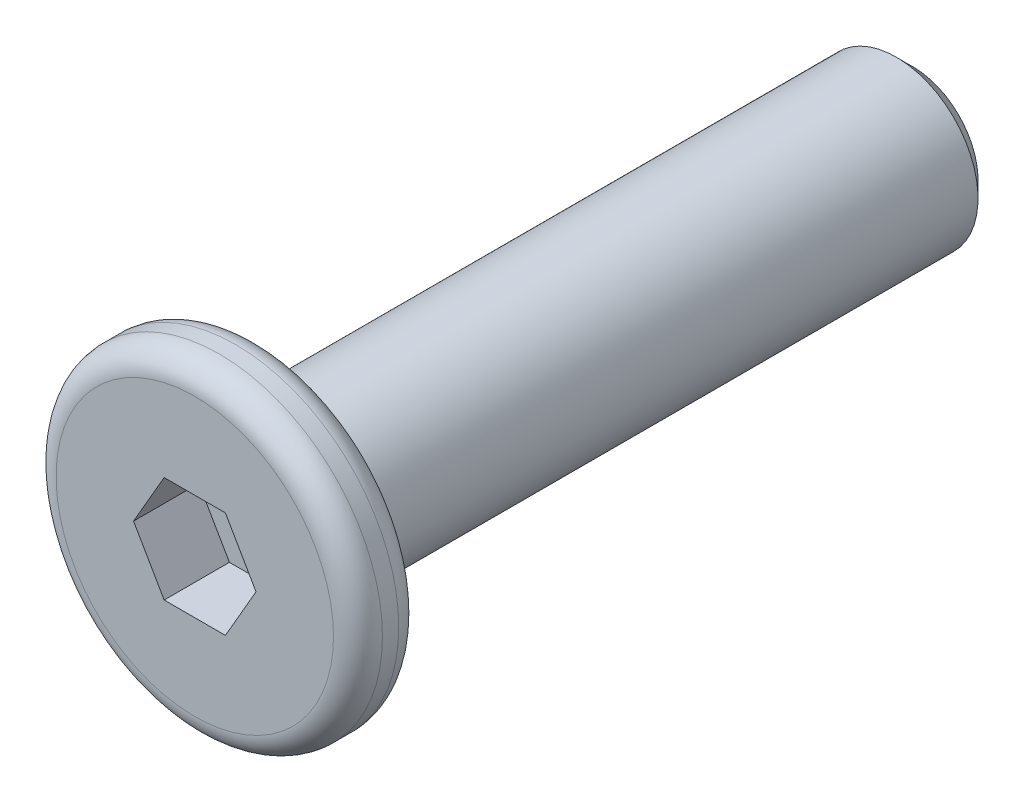
SolidWorks part; units mm, degrees
ref_plane "前视基准面" through (0, 0, 0) normal (0, 0, 1) x (1, 0, 0)
ref_plane "上视基准面" through (0, 0, 0) normal (0, 1, 0) x (1, 0, 0)
ref_plane "右视基准面" through (0, 0, 0) normal (1, 0, 0) x (0, 0, -1)
sketch "草图1" plane through (0, 0, 0) normal (0, 0, 1) x (1, 0, 0)
  circle A0 centre (0, 0) radius 2
  dimension "D1" = 4
extrude "凸台-拉伸1" add sketch "草图1" along normal mid plane 0.8
sketch "草图2" plane through (0, 0, -0.4) normal (0, 0, -1) x (-1, 0, 0)
  circle A0 centre (0, 0) radius 1
  dimension "D1" = 2
extrude "凸台-拉伸2" add sketch "草图2" along normal blind 8
chamfer "倒角1" distance 0.2 angle 45 1 edges at (-1, 0, -8.4)
sketch "草图3" plane through (0, 0, 0.4) normal (0, 0, 1) x (1, 0, 0)
  line L1 (0.7506, 0) -> (0.3753, 0.65)
  line L2 (0.3753, 0.65) -> (-0.3753, 0.65)
  line L3 (-0.3753, 0.65) -> (-0.7506, 0)
  line L4 (-0.7506, 0) -> (-0.3753, -0.65)
  line L5 (-0.3753, -0.65) -> (0.3753, -0.65)
  line L6 (0.3753, -0.65) -> (0.7506, 0)
  circle A0 centre (0, 0) radius 0.65 construction
  dimension "D1" = 1.3
extrude "切除-拉伸1" cut sketch "草图3" against normal blind 0.8
fillet "圆角2" radius 0.3 2 edges at (2, 0, -0.4) (2, 0, 0.4)
